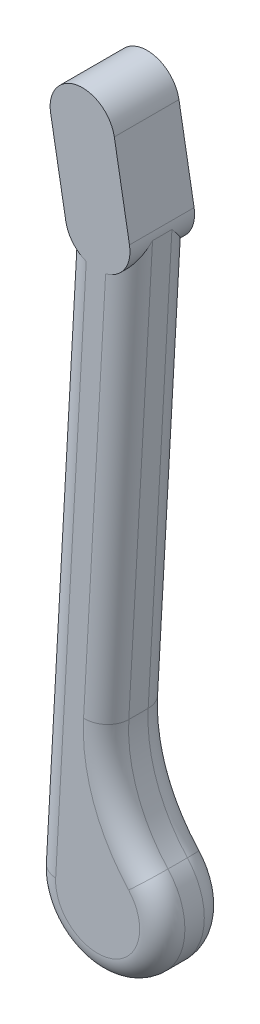
SolidWorks part; units mm, degrees
ref_plane "前视基准面" through (0, 0, 0) normal (0, 0, 1) x (1, 0, 0)
ref_plane "上视基准面" through (0, 0, 0) normal (0, 1, 0) x (1, 0, 0)
ref_plane "右视基准面" through (0, 0, 0) normal (1, 0, 0) x (0, 0, -1)
sketch "草图1" plane through (0, 0, 0) normal (0, 0, 1) x (1, 0, 0)
  line L2 (-9.9846, 0.5556) -> (-19.9691, -178.8889)
  line L3 (9.9846, -0.5556) -> (2.6417, -132.5229)
  arc A1 (2.6417, -132.5229) -> (14.7599, -166.5039) centre (49.0961, -135.1077) ccw
  arc A4 (-19.9691, -178.8889) -> (14.7599, -166.5039) centre (0, -180) ccw
  arc A5 (-9.9846, 0.5556) -> (9.9846, -0.5556) centre (0, 0) cw
extrude "凸台-拉伸1" add sketch "草图1" along normal blind 20
fillet "圆角1" radius 7 10 edges at (-14.9768, -89.1667, 0) (0.5556, 9.9846, 0) (6.3131, -66.5392, 0) (5.2731, -150.7358, 0) (-14.9768, -89.1667, 20) (0.5556, 9.9846, 20) (6.3131, -66.5392, 20) (5.2731, -150.7358, 20) (6.718, -198.838, 0) (6.718, -198.838, 20)
sketch "草图2" plane through (0, 0, 0) normal (0, 0, 1) x (1, 0, 0)
  line L0 (0, 0) -> (0, 27) construction
  line L4 (-4.6885, 26.5898) -> (0, 0) construction
  line L5 (5.1596, 28.3263) -> (9.8481, 1.7365)
  line L6 (-14.5366, 24.8533) -> (-9.8481, -1.7365)
  arc A8 (0, 27) -> (-4.6885, 26.5898) centre (0, 0) ccw construction
  arc A10 (5.1596, 28.3263) -> (-14.5366, 24.8533) centre (-4.6885, 26.5898) ccw
  arc A11 (-9.8481, -1.7365) -> (9.8481, 1.7365) centre (0, 0) ccw
  point P1 (-2.3443, 13.2949)
extrude "凸台-拉伸2" add sketch "草图2" along normal blind 20
